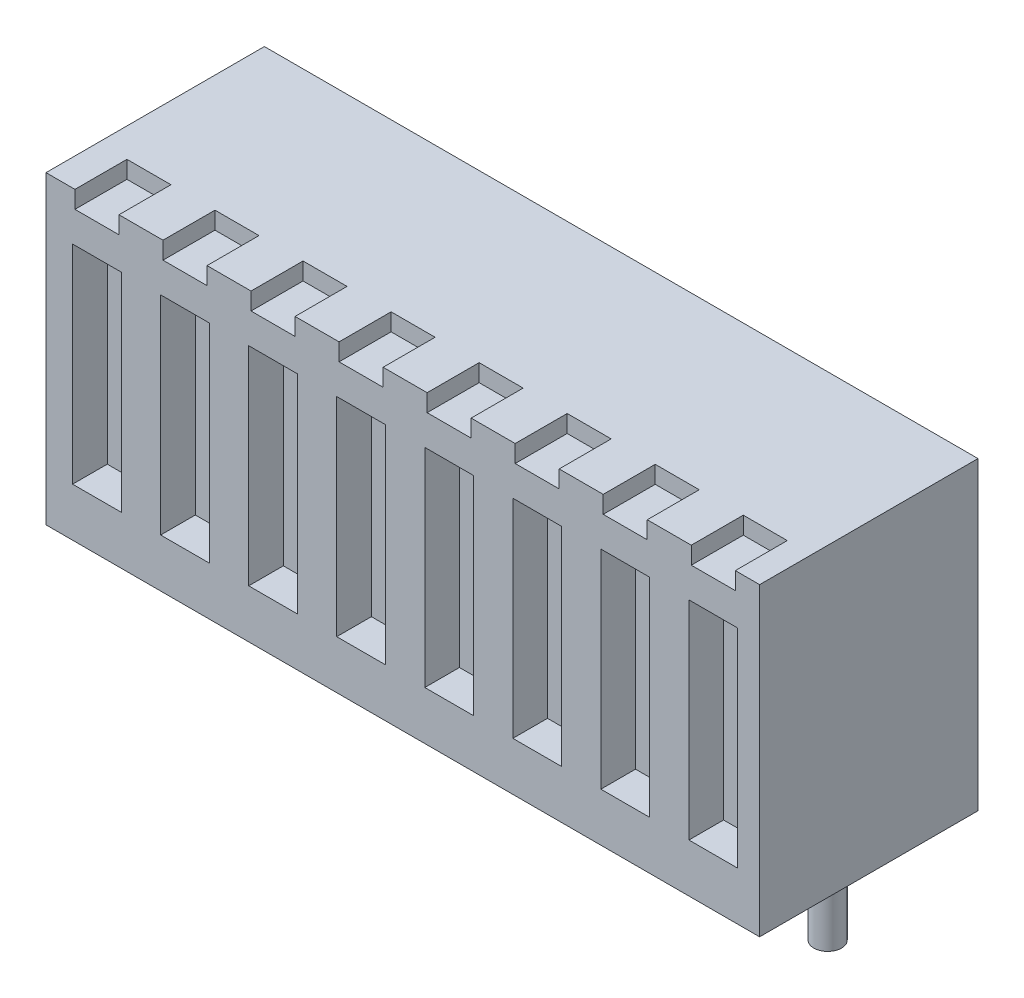
SolidWorks part; units mm, degrees
ref_plane "Front Plane" through (0, 0, 0) normal (0, 0, 1) x (1, 0, 0)
ref_plane "Top Plane" through (0, 0, 0) normal (0, 1, 0) x (1, 0, 0)
ref_plane "Right Plane" through (0, 0, 0) normal (1, 0, 0) x (0, 0, -1)
sketch "Sketch2" plane through (0, 0, 0) normal (0, 1, 0) x (1, 0, 0)
  line L1 (-10.2933, -3.15) -> (10.2933, -3.15)
  line L2 (-10.2933, -3.15) -> (-10.2933, 3.15)
  line L3 (-10.2933, 3.15) -> (10.2933, 3.15)
  line L4 (10.2933, -3.15) -> (10.2933, 3.15)
  line L5 (-10.2933, -3.15) -> (10.2933, 3.15) construction
  line L6 (-10.2933, 3.15) -> (10.2933, -3.15) construction
  point P0 (0, 0)
  dimension "D1" = 20.5867
  dimension "D2" = 6.3
extrude "Boss-Extrude1" add sketch "Sketch2" along normal blind 8.8
sketch "Sketch3" plane through (0, 0, 0) normal (0, -1, 0) x (1, 0, 0)
  line L0 (-10.2933, -3.15) -> (-10.2933, 3.15) construction
  line L1 (10.2933, -3.15) -> (-10.2933, -3.15) construction
  circle A0 centre (-8.8233, -0.15) radius 0.4
  dimension "D2" = 0.8
  dimension "D1" = 1.47
  dimension "D3" = 3
extrude "Boss-Extrude2" add sketch "Sketch3" along normal blind 2.4
sketch "Sketch4" plane through (0, 0, 3.15) normal (0, 0, 1) x (1, 0, 0)
  line L0 (-10.2933, 8.8) -> (-10.2933, 0) construction
  line L1 (-9.526, 7.4) -> (-8.1207, 7.4)
  line L2 (-9.526, 7.4) -> (-9.526, 1.4)
  line L3 (-9.526, 1.4) -> (-8.1207, 1.4)
  line L4 (-8.1207, 7.4) -> (-8.1207, 1.4)
  line L5 (-9.526, 7.4) -> (-8.1207, 1.4) construction
  line L6 (-9.526, 1.4) -> (-8.1207, 7.4) construction
  point P0 (-8.8233, 4.4)
  point P5 (-10.2933, 4.4)
  dimension "D1" = 6
  dimension "D2" = 1.4054
  dimension "D3" = 1.47
extrude "Cut-Extrude1" cut sketch "Sketch4" against normal blind 1
sketch "Sketch5" plane through (0, 8.8, 0) normal (0, 1, 0) x (1, 0, 0)
  line L0 (-10.2933, -3.15) -> (10.2933, -3.15) construction
  line L1 (-9.4583, -3.15) -> (-8.1883, -3.15)
  line L2 (-9.4583, -3.15) -> (-9.4583, -1.65)
  line L3 (-9.4583, -1.65) -> (-8.1883, -1.65)
  line L4 (-8.1883, -3.15) -> (-8.1883, -1.65)
  point P6 (-8.8233, -3.15)
  dimension "D1" = 1.5
  dimension "D2" = 1.27
  dimension "D3" = 1.47
extrude "Cut-Extrude2" cut sketch "Sketch5" against normal blind 0.5
pattern_linear "LPattern1" count 8 spacing 2.54 along (1, 0, 0) of "Boss-Extrude2", "Cut-Extrude1", "Cut-Extrude2"
equation "\"D1@Sketch2\"=30.88mm*8/12"
